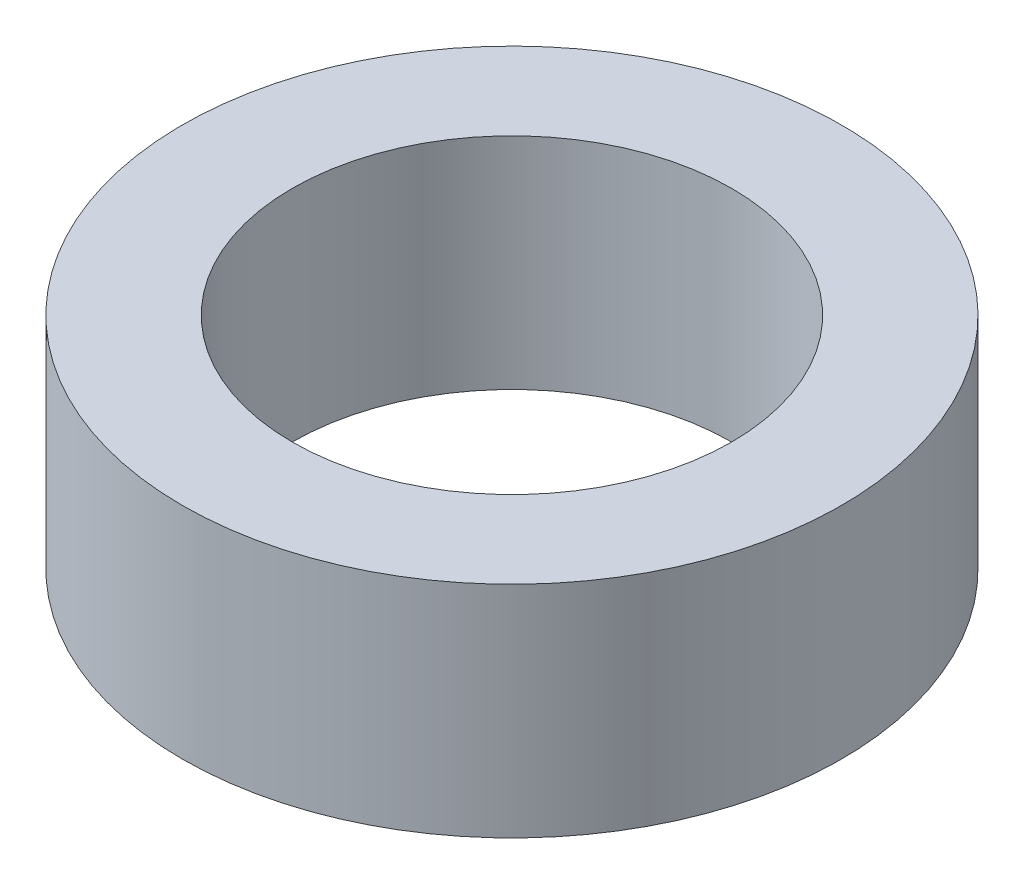
SolidWorks part; units mm, degrees
material "Cast Alloy Steel"
ref_plane "Front Plane" through (0, 0, 0) normal (0, 0, 1) x (1, 0, 0)
ref_plane "Top Plane" through (0, 0, 0) normal (0, 1, 0) x (1, 0, 0)
ref_plane "Right Plane" through (0, 0, 0) normal (1, 0, 0) x (0, 0, -1)
sketch "Sketch1" plane through (0, 0, 0) normal (0, 1, 0) x (1, 0, 0)
  circle A0 centre (0, 0) radius 3.175
  circle A1 centre (0, 0) radius 4.7625
  dimension "D1" = 6.35
  dimension "D2" = 9.525
extrude "Boss-Extrude1" add sketch "Sketch1" along normal blind 3.175
